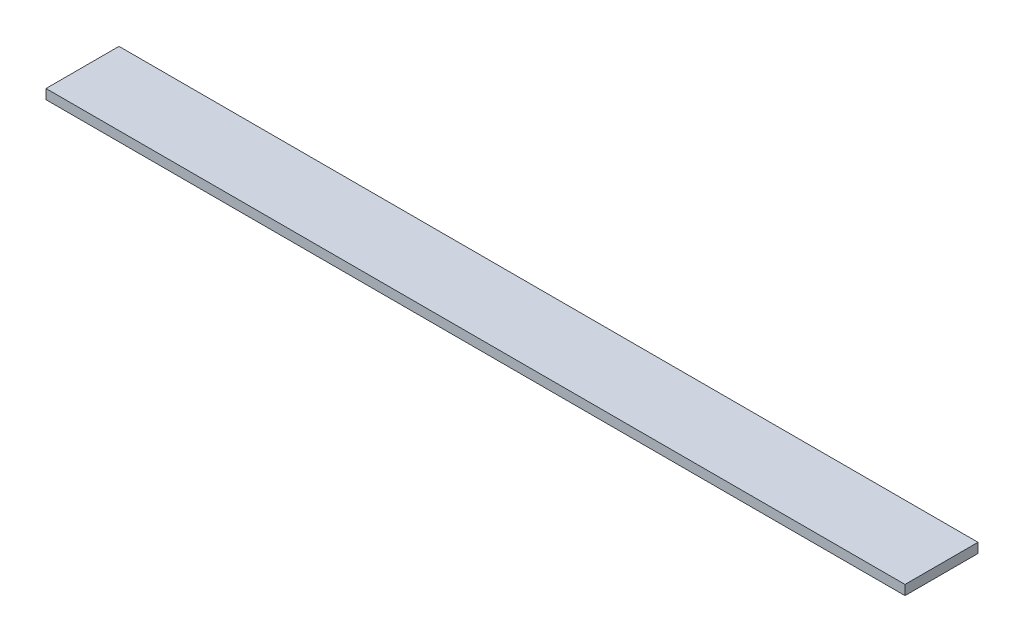
SolidWorks part; units mm, degrees
ref_plane "Спереди" through (0, 0, 0) normal (0, 0, 1) x (1, 0, 0)
ref_plane "Сверху" through (0, 0, 0) normal (0, 1, 0) x (1, 0, 0)
ref_plane "Справа" through (0, 0, 0) normal (1, 0, 0) x (0, 0, -1)
sketch "Эскиз1" plane through (0, 0, 0) normal (1, 0, 0) x (0, 0, -1)
  line L1 (-15, -2) -> (15, -2)
  line L2 (-15, -2) -> (-15, 2)
  line L3 (-15, 2) -> (15, 2)
  line L4 (15, -2) -> (15, 2)
  line L5 (-15, -2) -> (15, 2) construction
  line L6 (-15, 2) -> (15, -2) construction
  point P0 (0, 0)
  dimension "D1" = 4
  dimension "D2" = 30
extrude "Бобышка-Вытянуть1" add sketch "Эскиз1" along normal blind 353
